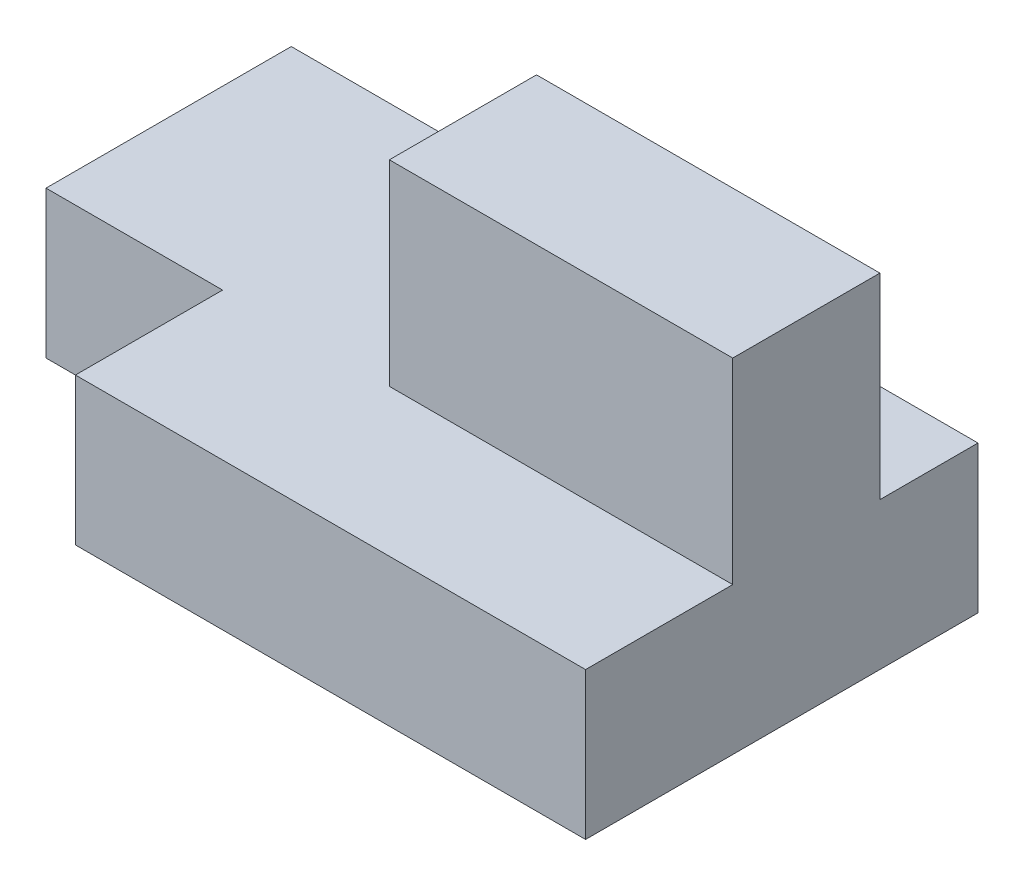
SolidWorks part; units mm, degrees
ref_plane "Ön Düzlem" through (0, 0, 0) normal (0, 0, 1) x (1, 0, 0)
ref_plane "Üst Düzlem" through (0, 0, 0) normal (0, 1, 0) x (1, 0, 0)
ref_plane "Sağ Düzlem" through (0, 0, 0) normal (1, 0, 0) x (0, 0, -1)
sketch "Sketch1" plane through (0, 0, 0) normal (0, 1, 0) x (1, 0, 0)
  line L1 (0, 0) -> (-70, 0)
  line L2 (0, 0) -> (0, -40)
  line L3 (0, -40) -> (-52, -40)
  line L4 (-70, 0) -> (-70, -25)
  line L7 (-70, -25) -> (-52, -25)
  line L8 (-52, -40) -> (-52, -25)
  dimension "D1" = 70
  dimension "D2" = 40
  dimension "D3" = 15
  dimension "D4" = 18
extrude "Boss-Extrude1" add sketch "Sketch1" along normal blind 15
sketch "Sketch2" plane through (0, 15, 0) normal (0, 1, 0) x (1, 0, 0)
  line L0 (0, -40) -> (0, 0) construction
  line L1 (0, -10) -> (-35, -10)
  line L2 (0, -10) -> (0, -25)
  line L3 (0, -25) -> (-35, -25)
  line L4 (-35, -10) -> (-35, -25)
  line L5 (0, 0) -> (-70, 0) construction
  dimension "D1" = 15
  dimension "D2" = 10
  dimension "D3" = 35
extrude "Boss-Extrude2" add sketch "Sketch2" along normal blind 20
